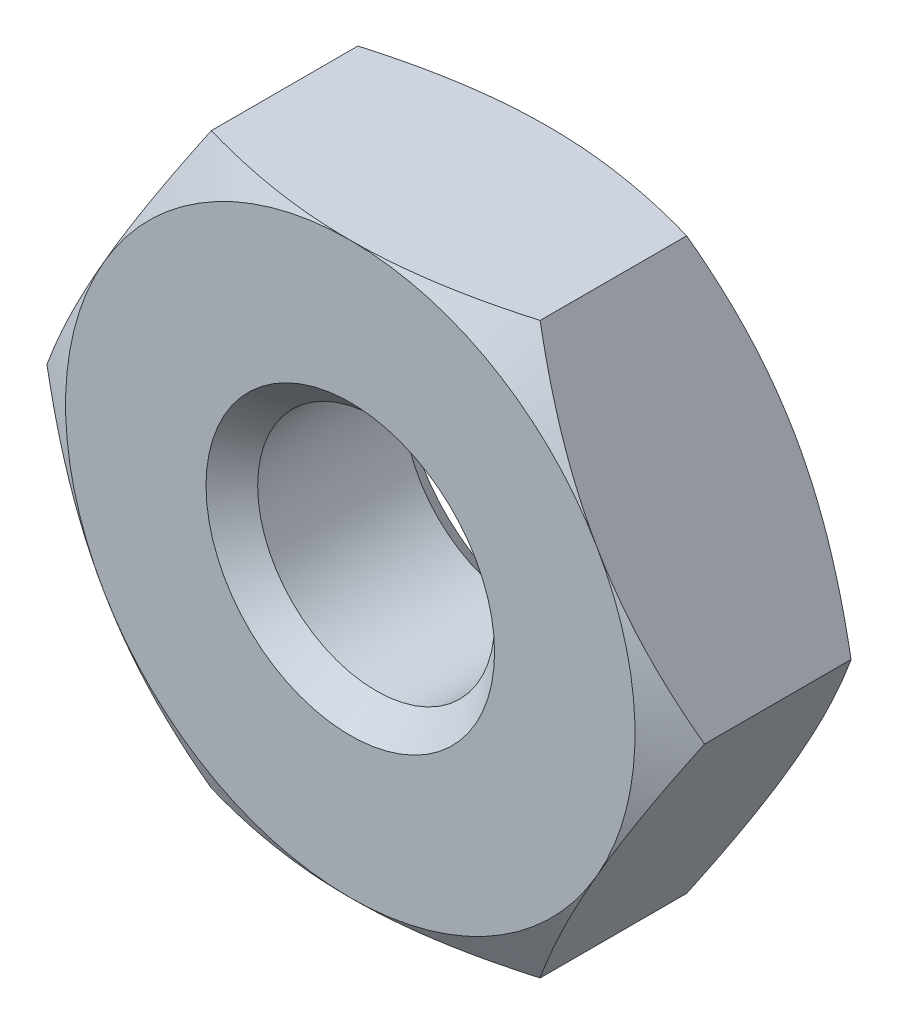
SolidWorks part; units mm, degrees
material "6061 Alloy"
ref_plane "Front Plane" through (0, 0, 0) normal (0, 0, 1) x (1, 0, 0)
ref_plane "Top Plane" through (0, 0, 0) normal (0, 1, 0) x (1, 0, 0)
ref_plane "Right Plane" through (0, 0, 0) normal (1, 0, 0) x (0, 0, -1)
sketch "Sketch1" plane through (0, 1.651, 0) normal (0, 0, -1) x (-1, 0, 0)
  line L1 (2.7496, 3.1115) -> (-2.7496, 3.1115)
  line L2 (-2.7496, 3.1115) -> (-5.4993, -1.651)
  line L3 (-5.4993, -1.651) -> (-2.7496, -6.4135)
  line L4 (-2.7496, -6.4135) -> (2.7496, -6.4135)
  line L5 (2.7496, -6.4135) -> (5.4993, -1.651)
  line L6 (5.4993, -1.651) -> (2.7496, 3.1115)
  circle A0 centre (0, -1.651) radius 4.7625 construction
  dimension "D1" = 9.525
extrude "Boss-Extrude1" add sketch "Sketch1" against normal mid plane 3.302
sketch "Sketch2" plane through (0, 0, 0) normal (0, 1, 0) x (-1, 0, 0)
  line L0 (-5.4993, -1.2256) -> (-5.4993, -1.651)
  line L1 (-5.4993, -1.651) -> (-4.7625, -1.651)
  line L2 (-4.7625, -1.651) -> (-5.4993, -1.2256)
  line L3 (0, 0) -> (0, -1.651) construction
  line L4 (-5.4993, 1.651) -> (-5.4993, -1.651) construction
  line L5 (-2.7496, -1.651) -> (-5.4993, -1.651) construction
  dimension "D1" = 0.7368
  dimension "D2" = 5.4993
  dimension "D3" = 0.4254
revolve "Cut-Revolve1" cut sketch "Sketch2" angle 360 about L3
sketch "Sketch4" plane through (0, 0, 0) normal (0, 1, 0) x (1, 0, 0)
  line L0 (2.413, 1.651) -> (0, 1.651)
  line L1 (0, 1.651) -> (0, -1.2192)
  line L2 (0, -1.2192) -> (1.9812, -1.2192)
  line L3 (1.9812, -1.2192) -> (1.9812, 1.2192)
  line L4 (1.9812, 1.2192) -> (2.413, 1.651)
  line L5 (0, 1.651) -> (0, -1.2192) construction
  line L6 (4.1244, 1.651) -> (0, 1.651) construction
  dimension "D1" = 1.9812
  dimension "D2" = 2.413
  dimension "D3" = 0.4318
  dimension "D4" = 2.8702
revolve "Cut-Revolve3" cut sketch "Sketch4" angle 360 about L5
mirror "Mirror1" about plane through (0, 0, 0) normal (0, 0, 1) of "Cut-Revolve1", "Cut-Revolve3"
